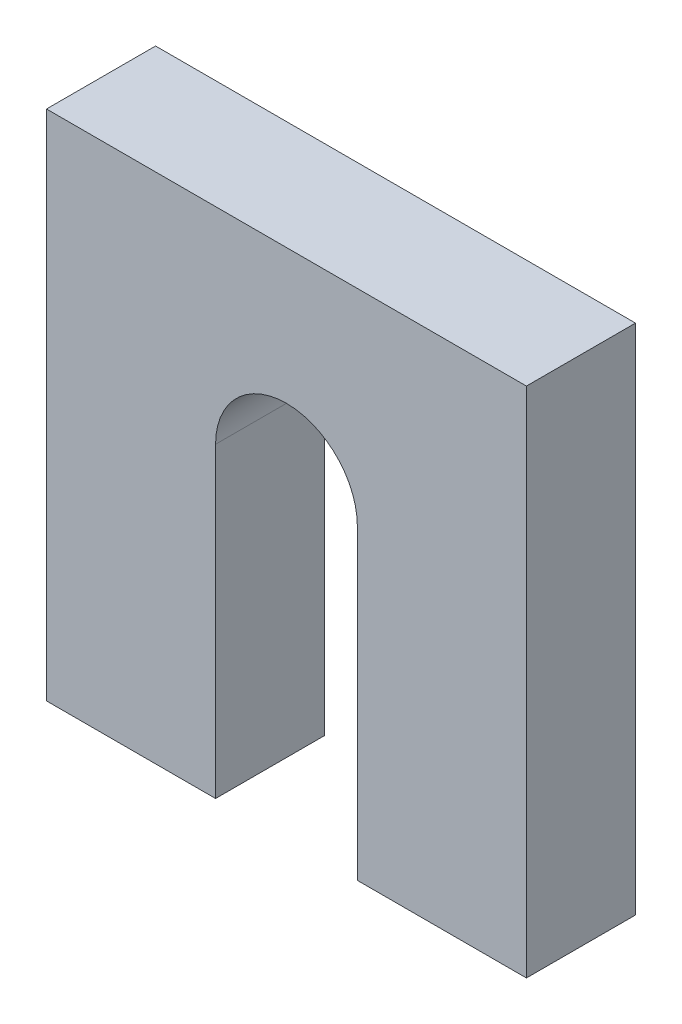
SolidWorks part; units mm, degrees
ref_plane "Front Plane" through (0, 0, 0) normal (0, 0, 1) x (1, 0, 0)
ref_plane "Top Plane" through (0, 0, 0) normal (0, 1, 0) x (1, 0, 0)
ref_plane "Right Plane" through (0, 0, 0) normal (1, 0, 0) x (0, 0, -1)
sketch "Sketch2" plane through (0, 0, 0) normal (0, 0, 1) x (1, 0, 0)
  line L1 (22, 23.5) -> (-22, 23.5)
  line L2 (22, 23.5) -> (22, -23.5)
  line L3 (22, -23.5) -> (-22, -23.5)
  line L4 (-22, 23.5) -> (-22, -23.5)
  line L5 (22, 23.5) -> (-22, -23.5) construction
  line L6 (22, -23.5) -> (-22, 23.5) construction
  point P0 (0, 0)
  dimension "D1" = 44
  dimension "D2" = 47
extrude "Boss-Extrude1" add sketch "Sketch2" along normal blind 10
sketch "Sketch3" plane through (0, 0, 10) normal (0, 0, 1) x (1, 0, 0)
  line L0 (0, -23.5) -> (0, 4.6283) construction
  line L1 (-22, -23.5) -> (22, -23.5) construction
  line L2 (-6.5, -23.5) -> (-6.5, 4.6283)
  line L3 (6.5, -23.5) -> (6.5, 4.6283)
  arc A0 (-6.5, -23.5) -> (6.5, -23.5) centre (0, -23.5) ccw
  arc A1 (6.5, 4.6283) -> (-6.5, 4.6283) centre (0, 4.6283) ccw
  point P5 (0, -9.4359)
  dimension "D1" = 13
extrude "Cut-Extrude1" cut sketch "Sketch3" against normal blind 10
